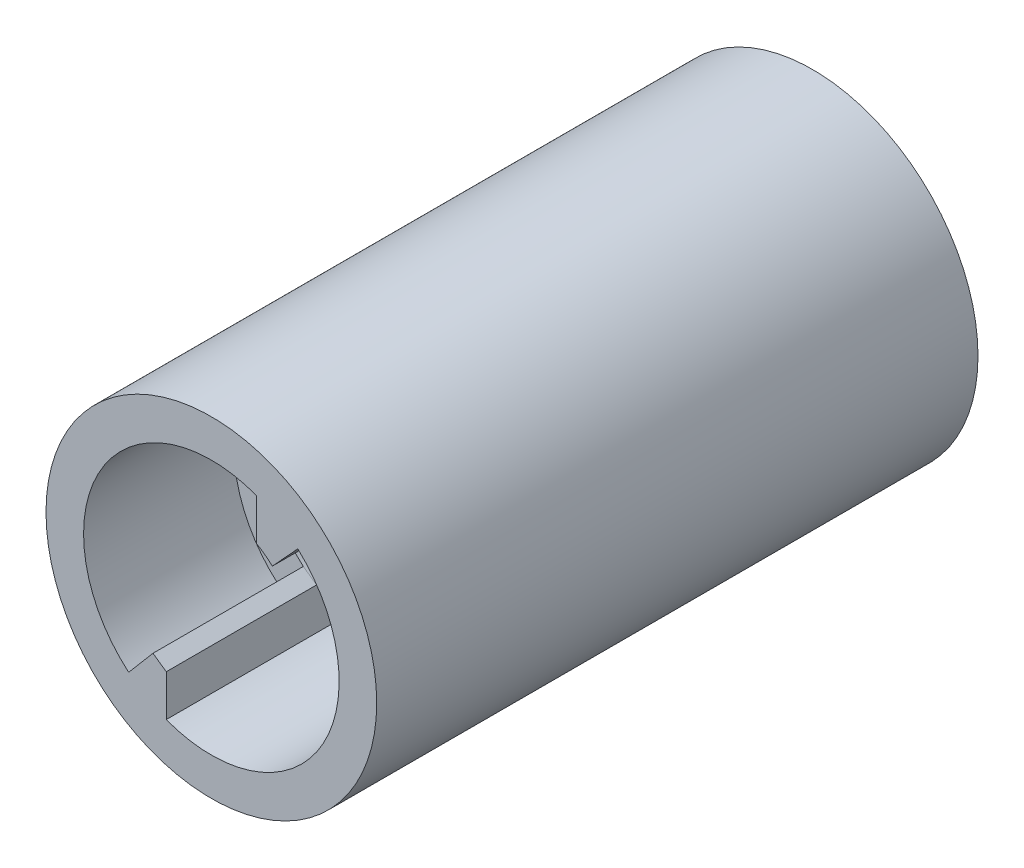
SolidWorks part; units mm, degrees
ref_plane "Alzado" through (0, 0, 0) normal (0, 0, 1) x (1, 0, 0)
ref_plane "Planta" through (0, 0, 0) normal (0, 1, 0) x (1, 0, 0)
ref_plane "Vista lateral" through (0, 0, 0) normal (1, 0, 0) x (0, 0, -1)
sketch "Croquis1" plane through (0, 0, 0) normal (0, 0, 1) x (1, 0, 0)
  circle A0 centre (0, 0) radius 11
  circle A1 centre (0, 0) radius 6
  dimension "D1" = 22
  dimension "D2" = 12
extrude "Saliente-Extruir1" add sketch "Croquis1" along normal blind 25
sketch "Croquis2" plane through (0, 0, 25) normal (0, 0, 1) x (1, 0, 0)
  line L1 (-3, 11) -> (3, 11)
  line L2 (-3, 11) -> (-3, -11)
  line L3 (-3, -11) -> (3, -11)
  line L4 (3, 11) -> (3, -11)
  line L5 (-3, 11) -> (3, -11) construction
  line L6 (-3, -11) -> (3, 11) construction
  point P0 (0, 0)
  dimension "D1" = 22
  dimension "D2" = 6
extrude "Cortar-Extruir1" cut sketch "Croquis2" against normal blind 25
sketch "Croquis3" plane through (0, 0, 0) normal (0, 0, 1) x (1, 0, 0)
  circle A0 centre (0, 0) radius 11
  circle A1 centre (0, 0) radius 8.5
  dimension "D1" = 22
  dimension "D2" = 17
extrude "Saliente-Extruir2" add sketch "Croquis3" along normal blind 25
sketch "Croquis4" plane through (0, 0, 25) normal (0, 0, 1) x (1, 0, 0)
  line L0 (3, 5.1962) -> (3, 10.583)
  line L1 (4.0592, 4.4184) -> (7.4419, 8.1005)
  circle A0 centre (0, 0) radius 11 construction
  arc A1 (3, -5.1962) -> (3, 5.1962) centre (0, 0) ccw construction
  arc A2 (3, 5.1962) -> (4.0592, 4.4184) centre (0, 0) cw
  arc A3 (3, 10.583) -> (7.4419, 8.1005) centre (0, 0) cw
extrude "Saliente-Extruir3" add sketch "Croquis4" along normal blind 10
sketch "Croquis5" plane through (0, 0, 25) normal (0, 0, 1) x (1, 0, 0)
  line L0 (-3, -5.1962) -> (-3, -10.583)
  line L1 (-7.1194, -8.3854) -> (-3.8833, -4.5738)
  arc A0 (3, 10.583) -> (7.4419, 8.1005) centre (0, 0) ccw construction
  arc A1 (-3, 5.1962) -> (-3, -5.1962) centre (0, 0) ccw construction
  arc A2 (-3.8833, -4.5738) -> (-3, -5.1962) centre (0, 0) ccw
  arc A3 (-7.1194, -8.3854) -> (-3, -10.583) centre (0, 0) ccw
sketch "Croquis8" plane through (0, 0, 25) normal (0, 0, 1) x (1, 0, 0)
  line L0 (-3, -10.583) -> (-3, -5.1962)
  line L1 (-3, -5.1962) -> (-3.8833, -4.5738)
  line L2 (-3, -10.583) -> (-7.1194, -8.3854)
  line L3 (-7.1194, -8.3854) -> (-3.8833, -4.5738)
extrude "Saliente-Extruir4" add sketch "Croquis8" along normal blind 10
sketch "Croquis9" plane through (0, 0, 25) normal (0, 0, 1) x (1, 0, 0)
  circle A0 centre (0, 0) radius 8.5
  circle A1 centre (0, 0) radius 11
  dimension "D1" = 22
  dimension "D2" = 17
extrude "Saliente-Extruir5" add sketch "Croquis9" along normal blind 10
sketch "Croquis13" plane through (0, 0, 0) normal (0, 0, -1) x (-1, 0, 0)
  circle A0 centre (0, 0) radius 11
  circle A1 centre (0, 0) radius 6
extrude "Saliente-Extruir6" add sketch "Croquis13" along normal blind 5
sketch "Croquis14" plane through (0, 0, -5) normal (0, 0, -1) x (-1, 0, 0)
  line L1 (3, 11) -> (-3, 11)
  line L2 (3, 11) -> (3, -11)
  line L3 (3, -11) -> (-3, -11)
  line L4 (-3, 11) -> (-3, -11)
  line L5 (3, 11) -> (-3, -11) construction
  line L6 (3, -11) -> (-3, 11) construction
  point P0 (0, 0)
  dimension "D1" = 6
  dimension "D2" = 22
extrude "Cortar-Extruir2" cut sketch "Croquis14" against normal blind 5
sketch "Croquis15" plane through (0, 0, -5) normal (0, 0, -1) x (-1, 0, 0)
  circle A0 centre (0, 0) radius 8.5
  circle A1 centre (0, 0) radius 11
  dimension "D1" = 17
extrude "Saliente-Extruir7" add sketch "Croquis15" against normal blind 5
